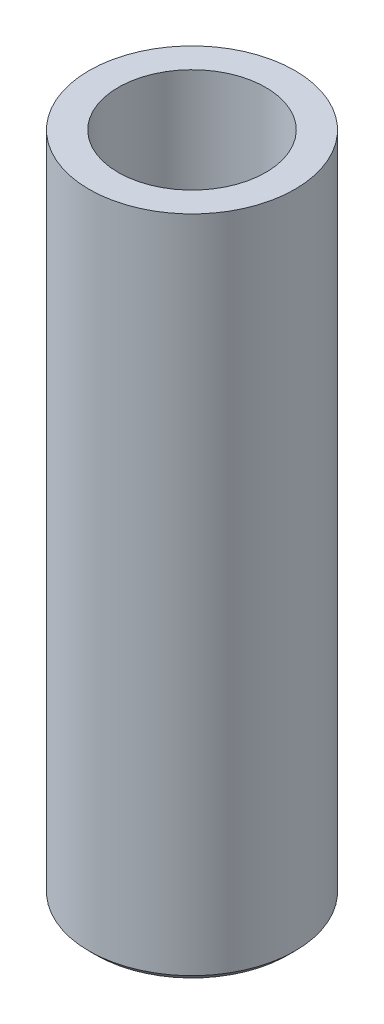
SolidWorks part; units mm, degrees
ref_plane "Front" through (0, 0, 0) normal (0, 0, 1) x (1, 0, 0)
ref_plane "Top" through (0, 0, 0) normal (0, 1, 0) x (1, 0, 0)
ref_plane "Right" through (0, 0, 0) normal (1, 0, 0) x (0, 0, -1)
sketch "Sketch1" plane through (0, 0, 0) normal (0, 1, 0) x (1, 0, 0)
  circle A0 centre (0, 0) radius 6
  dimension "D1" = 12
extrude "Boss-Extrude1" add sketch "Sketch1" along normal blind 1
sketch "Sketch2" plane through (0, 1, 0) normal (0, 1, 0) x (1, 0, 0)
  circle A0 centre (0, 0) radius 4.3
  circle A1 centre (0, 0) radius 6 construction
  circle A2 centre (0, 0) radius 6
  dimension "D1" = 8.6
extrude "Boss-Extrude2" add sketch "Sketch2" along normal blind 37.86
chamfer "Chamfer1" distance 0.4 angle 45 1 edges at (0, 0, 6)
